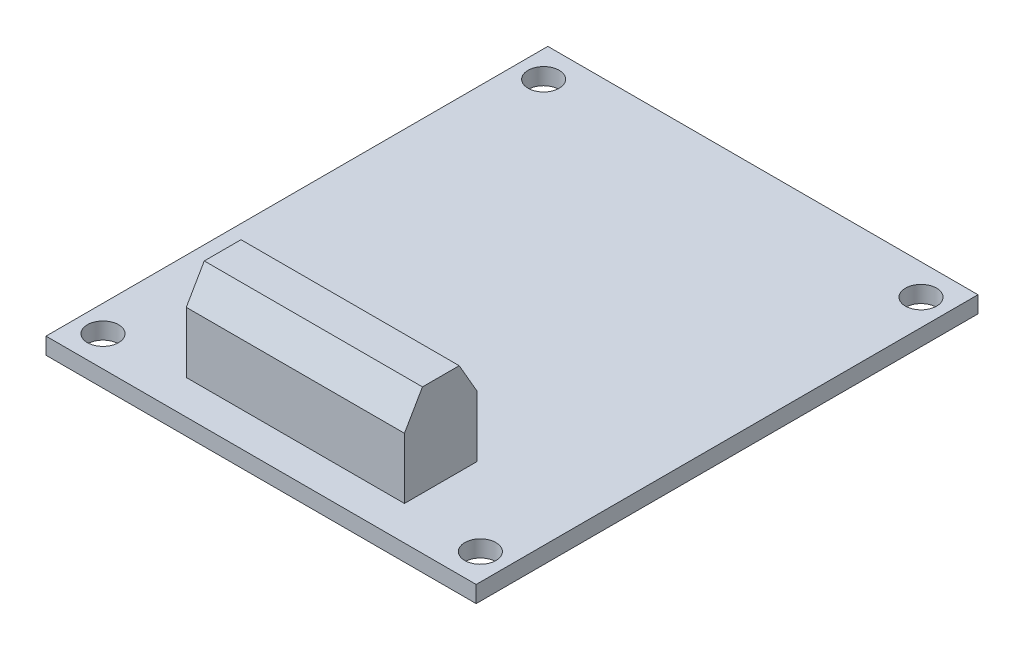
SolidWorks part; units mm, degrees
ref_plane "Front Plane" through (0, 0, 0) normal (0, 0, 1) x (1, 0, 0)
ref_plane "Top Plane" through (0, 0, 0) normal (0, 1, 0) x (1, 0, 0)
ref_plane "Right Plane" through (0, 0, 0) normal (1, 0, 0) x (0, 0, -1)
sketch "Sketch1" plane through (0, 0, 0) normal (0, 1, 0) x (1, 0, 0)
  line L0 (0, 24.15) -> (0, -24.15) construction
  line L1 (20.7, 24.15) -> (-20.7, 24.15)
  line L2 (20.7, 24.15) -> (20.7, -24.15)
  line L3 (20.7, -24.15) -> (-20.7, -24.15)
  line L4 (-20.7, 24.15) -> (-20.7, -24.15)
  line L5 (20.7, 24.15) -> (-20.7, -24.15) construction
  line L6 (20.7, -24.15) -> (-20.7, 24.15) construction
  line L7 (-20.7, 0) -> (20.7, 0) construction
  circle A0 centre (-18.16, 21.205) radius 1.5
  circle A1 centre (18.16, 21.205) radius 1.5
  circle A2 centre (18.16, -21.205) radius 1.5
  circle A3 centre (-18.16, -21.205) radius 1.5
  point P0 (0, 0)
  dimension "D3" = 3
  dimension "D4" = 36.32
  dimension "D1" = 48.3
  dimension "D2" = 41.4
  dimension "D5" = 42.41
extrude "Boss-Extrude1" add sketch "Sketch1" along normal blind 1.6
sketch "Sketch2" plane through (0, 1.6, 0) normal (0, 1, 0) x (1, 0, 0)
  line L0 (0, 24.15) -> (0, -24.15) construction
  line L1 (20.7, 24.15) -> (-20.7, 24.15) construction
  line L2 (-20.7, -24.15) -> (20.7, -24.15) construction
  line L7 (-10.5, -13.85) -> (10.5, -13.85)
  line L8 (-10.5, -13.85) -> (-10.5, -20.85)
  line L9 (-10.5, -20.85) -> (10.5, -20.85)
  line L10 (10.5, -13.85) -> (10.5, -20.85)
  line L11 (-10.5, -13.85) -> (10.5, -20.85) construction
  line L12 (-10.5, -20.85) -> (10.5, -13.85) construction
  point P12 (0, -17.35)
  dimension "D1" = 7
  dimension "D2" = 21
  dimension "D3" = 3.3
extrude "Boss-Extrude2" add sketch "Sketch2" along normal blind 8.85
chamfer "Chamfer1" distance 3 angle 30 2 edges at (0, 10.45, 13.85) (0, 10.45, 20.85)
